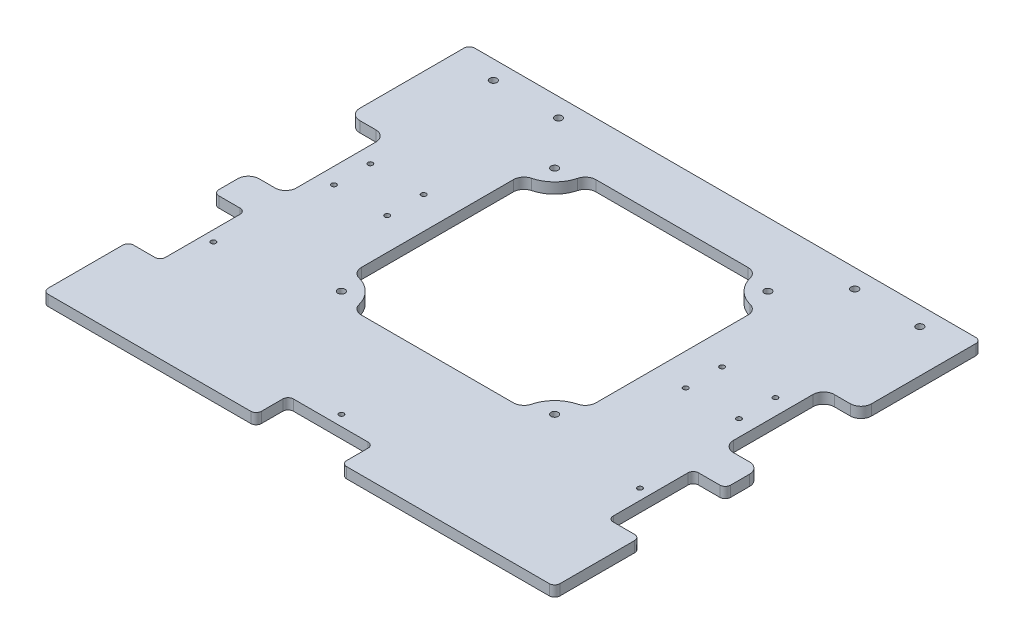
SolidWorks part; units mm, degrees
ref_plane "Front Plane" through (0, 0, 0) normal (0, 0, 1) x (1, 0, 0)
ref_plane "Top Plane" through (0, 0, 0) normal (0, 1, 0) x (1, 0, 0)
ref_plane "Right Plane" through (0, 0, 0) normal (1, 0, 0) x (0, 0, -1)
sketch "Footprint" plane through (0, 0, 0) normal (0, 1, 0) x (1, 0, 0)
  line L1 (-177.8, -177.8) -> (177.8, -177.8) construction
  line L2 (-177.8, -177.8) -> (-177.8, 177.8) construction
  line L3 (-177.8, 177.8) -> (177.8, 177.8) construction
  line L4 (177.8, -177.8) -> (177.8, 177.8) construction
  line L5 (-177.8, -177.8) -> (177.8, 177.8) construction
  line L6 (-177.8, 177.8) -> (177.8, -177.8) construction
  point P0 (0, 0)
  dimension "D1" = 355.6
  dimension "D2" = 355.6
sketch "Sketch2" plane through (0, 0, 0) normal (0, 1, 0) x (1, 0, 0)
  line L1 (-152.4, -152.4) -> (152.4, -152.4)
  line L2 (-152.4, -152.4) -> (-152.4, 101.6)
  line L3 (-152.4, 101.6) -> (152.4, 101.6)
  line L4 (152.4, -152.4) -> (152.4, 101.6)
  line L6 (0, 101.6) -> (0, 0) construction
  dimension "D1" = 254
  dimension "D2" = 304.8
  dimension "D3" = 101.6
extrude "Base" add sketch "Sketch2" along normal blind 6.35
sketch "Sketch5" plane through (0, 6.35, 0) normal (0, 1, 0) x (1, 0, 0)
  line L1 (-69.85, -69.85) -> (69.85, -69.85)
  line L2 (-69.85, -69.85) -> (-69.85, 69.85)
  line L3 (-69.85, 69.85) -> (69.85, 69.85)
  line L4 (69.85, -69.85) -> (69.85, 69.85)
  line L5 (-69.85, -69.85) -> (69.85, 69.85) construction
  line L6 (-69.85, 69.85) -> (69.85, -69.85) construction
  point P0 (0, 0)
  dimension "D1" = 139.7
  dimension "D2" = 139.7
extrude "Fan Cutout" cut sketch "Sketch5" against normal up to surface (6.35 mm away) up to face at (0, 0, 25.4)
sketch "Sketch7" plane through (0, 6.35, 0) normal (0, 1, 0) x (1, 0, 0)
  line L0 (-69.85, 50.8) -> (-69.85, 69.85)
  line L1 (50.8, 69.85) -> (69.85, 69.85)
  line L2 (-69.85, 69.85) -> (-69.85, -69.85) construction
  line L3 (-69.85, 69.85) -> (-50.8, 69.85)
  line L4 (69.85, 69.85) -> (69.85, 50.8)
  line L5 (69.85, 69.85) -> (-69.85, 69.85) construction
  line L6 (69.85, -69.85) -> (69.85, 69.85) construction
  line L7 (-69.85, -50.8) -> (-69.85, -69.85)
  line L8 (-69.85, -69.85) -> (-50.8, -69.85)
  line L9 (-69.85, -69.85) -> (69.85, -69.85) construction
  line L10 (50.8, -69.85) -> (69.85, -69.85)
  line L11 (69.85, -69.85) -> (69.85, -50.8)
  arc A0 (-69.85, 50.8) -> (-50.8, 69.85) centre (-69.85, 69.85) ccw
  arc A1 (50.8, 69.85) -> (69.85, 50.8) centre (69.85, 69.85) ccw
  arc A2 (-69.85, -50.8) -> (-50.8, -69.85) centre (-69.85, -69.85) cw
  arc A3 (50.8, -69.85) -> (69.85, -50.8) centre (69.85, -69.85) cw
  dimension "D3" = 19.05
  dimension "D6" = 19.05
  dimension "D9" = 19.05
  dimension "D12" = 19.05
  dimension "D1" = 19.05
  dimension "D2" = 19.05
  dimension "D4" = 19.05
  dimension "D5" = 19.05
  dimension "D7" = 19.05
  dimension "D8" = 19.05
  dimension "D10" = 19.05
  dimension "D11" = 19.05
extrude "Boss-Extrude1" add sketch "Sketch7" against normal up to surface (6.35 mm away) up to face at (0, 0, 0)
sketch "Sketch8" plane through (0, 6.35, 0) normal (0, 1, 0) x (1, 0, 0)
  line L0 (-69.85, 50.8) -> (-69.85, -50.8) construction
  line L1 (-63.5, -63.5) -> (63.5, -63.5) construction
  line L2 (-63.5, -63.5) -> (-63.5, 63.5) construction
  line L3 (-63.5, 63.5) -> (63.5, 63.5) construction
  line L4 (63.5, -63.5) -> (63.5, 63.5) construction
  line L5 (-63.5, -63.5) -> (63.5, 63.5) construction
  line L6 (-63.5, 63.5) -> (63.5, -63.5) construction
  line L7 (50.8, 69.85) -> (-50.8, 69.85) construction
  circle A0 centre (-63.5, 63.5) radius 2.1527
  circle A1 centre (63.5, 63.5) radius 2.1527
  circle A2 centre (63.5, -63.5) radius 2.1527
  circle A3 centre (-63.5, -63.5) radius 2.1527
  point P8 (0, 0)
  dimension "D1" = 4.3053
  dimension "D2" = 6.35
  dimension "D3" = 6.35
extrude "Cut-Extrude1" cut sketch "Sketch8" against normal up to surface (6.35 mm away) up to face at (0, 0, 0)
fillet "Fillet2" radius 6.35 8 edges at (69.85, 3.175, 50.8) (50.8, 3.175, 69.85) (69.85, 3.175, -50.8) (50.8, 3.175, -69.85) (-50.8, 3.175, 69.85) (-69.85, 3.175, 50.8) (-69.85, 3.175, -50.8) (-50.8, 3.175, -69.85)
sketch "Sketch3" plane through (0, 6.35, 0) normal (0, 1, 0) x (1, 0, 0)
  line L0 (-152.4, 101.6) -> (-152.4, -152.4) construction
  line L1 (-130.175, -30) -> (-152.4, -30)
  line L2 (-130.175, -30) -> (-130.175, 30)
  line L3 (-130.175, 30) -> (-152.4, 30)
  line L4 (-152.4, -30) -> (-152.4, 30)
  line L5 (-130.175, -30) -> (-152.4, 30) construction
  line L6 (-130.175, 30) -> (-152.4, -30) construction
  line L7 (152.4, -152.4) -> (152.4, 101.6) construction
  line L8 (130.175, -30) -> (152.4, -30)
  line L9 (130.175, -30) -> (130.175, 30)
  line L10 (130.175, 30) -> (152.4, 30)
  line L11 (152.4, -30) -> (152.4, 30)
  line L12 (130.175, -30) -> (152.4, 30) construction
  line L13 (130.175, 30) -> (152.4, -30) construction
  line L14 (-141.2875, 0) -> (141.2875, 0) construction
  point P0 (-141.2875, 0)
  point P7 (141.2875, 0)
  dimension "D1" = 60
  dimension "D2" = 22.225
extrude "Wheel Cutouts" cut sketch "Sketch3" against normal up to surface (6.35 mm away) up to face at (-63.5, 0, 61.3473)
fillet "Wheel Fillets" radius 6.35 8 edges at (152.4, 3.175, 30) (130.175, 3.175, 30) (130.175, 3.175, -30) (152.4, 3.175, -30) (-152.4, 3.175, 30) (-130.175, 3.175, 30) (-130.175, 3.175, -30) (-152.4, 3.175, -30)
sketch "Sketch4" plane through (0, 6.35, 0) normal (0, 1, 0) x (1, 0, 0)
  line L0 (-152.4, 101.6) -> (-152.4, 36.35) construction
  line L1 (-152.4, -50.8) -> (-133.35, -50.8)
  line L2 (-152.4, -50.8) -> (-152.4, -101.6)
  line L3 (-152.4, -101.6) -> (-133.35, -101.6)
  line L4 (-133.35, -50.8) -> (-133.35, -101.6)
  line L5 (152.4, -152.4) -> (152.4, -36.35) construction
  line L6 (152.4, -50.8) -> (133.35, -50.8)
  line L7 (152.4, -50.8) -> (152.4, -101.6)
  line L8 (152.4, -101.6) -> (133.35, -101.6)
  line L9 (133.35, -50.8) -> (133.35, -101.6)
  line L10 (-152.4, -152.4) -> (152.4, -152.4) construction
  line L11 (-25.4, -152.4) -> (25.4, -152.4)
  line L12 (-25.4, -152.4) -> (-25.4, -133.35)
  line L13 (-25.4, -133.35) -> (25.4, -133.35)
  line L14 (25.4, -152.4) -> (25.4, -133.35)
  line L15 (-133.35, -76.2) -> (-127, -76.2) construction
  line L16 (127, -76.2) -> (133.35, -76.2) construction
  line L17 (0, 0) -> (0, -133.35) construction
  circle A0 centre (-127, -76.2) radius 1.4732
  circle A1 centre (127, -76.2) radius 1.4732
  circle A2 centre (0, -127) radius 1.4732
  dimension "D9" = 2.9464
  dimension "D1" = 19.05
  dimension "D2" = 50.8
  dimension "D3" = 19.05
  dimension "D4" = 50.8
  dimension "D5" = 50.8
  dimension "D6" = 19.05
  dimension "D7" = 50.8
  dimension "D8" = 50.8
  dimension "D10" = 6.35
  dimension "D11" = 6.35
  dimension "D12" = 6.35
extrude "Ultrasonic Cutouts" cut sketch "Sketch4" against normal up to surface (6.35 mm away) up to face at (0, 0, 5.08)
fillet "Ultrasonic Fillets" radius 3.175 12 edges at (152.4, 3.175, 50.8) (133.35, 3.175, 50.8) (133.35, 3.175, 101.6) (152.4, 3.175, 101.6) (25.4, 3.175, 152.4) (25.4, 3.175, 133.35) (-25.4, 3.175, 133.35) (-25.4, 3.175, 152.4) (-152.4, 3.175, 101.6) (-133.35, 3.175, 101.6) (-152.4, 3.175, 50.8) (-133.35, 3.175, 50.8)
sketch "Sketch6" plane through (0, 6.35, 0) normal (0, 1, 0) x (1, 0, 0)
  line L0 (152.4, 101.6) -> (50.8, 101.6) construction
  line L1 (152.4, 101.6) -> (-152.4, 101.6) construction
  line L2 (50.8, 101.6) -> (-50.8, 101.6) construction
  line L3 (-50.8, 101.6) -> (-152.4, 101.6) construction
  line L4 (50.8, 101.6) -> (50.8, -152.4) construction
  line L5 (28.575, -152.4) -> (152.4, -152.4) construction
  line L6 (-50.8, 101.6) -> (-50.8, -152.4) construction
  line L7 (-152.4, -152.4) -> (-28.575, -152.4) construction
fillet "Fillet3" radius 3.175 4 edges at (-152.4, 3.175, 152.4) (152.4, 3.175, 152.4) (152.4, 3.175, -101.6) (-152.4, 3.175, -101.6)
sketch "Sketch9" plane through (0, 6.35, 0) normal (0, 1, 0) x (1, 0, 0)
  line L0 (-127, 90.4875) -> (-88.2, 90.4875) construction
  line L1 (149.225, 101.6) -> (-149.225, 101.6) construction
  line L2 (88.2, 90.4875) -> (127, 90.4875) construction
  line L3 (-152.4, 98.425) -> (-152.4, 36.35) construction
  line L4 (152.4, 36.35) -> (152.4, 98.425) construction
  circle A0 centre (-127, 90.4875) radius 2.1527
  circle A1 centre (-88.2, 90.4875) radius 2.1527
  circle A2 centre (88.2, 90.4875) radius 2.1527
  circle A3 centre (127, 90.4875) radius 2.1527
  dimension "D1" = 4.3053
  dimension "D2" = 38.8
  dimension "D3" = 38.8
  dimension "D4" = 11.1125
  dimension "D5" = 11.1125
  dimension "D6" = 25.4
  dimension "D7" = 25.4
extrude "Cut-Extrude2" cut sketch "Sketch9" against normal up to surface (6.35 mm away) up to face at (0, 0, 125.5268)
sketch "Sketch10" plane through (0, 6.35, 0) normal (0, 1, 0) x (1, 0, 0)
  circle A0 centre (-120.625, 10.85) radius 1.4732
  circle A1 centre (-88.875, 10.85) radius 1.4732
  circle A2 centre (-120.625, -10.85) radius 1.4732
  circle A3 centre (-88.875, -10.85) radius 1.4732
  circle A4 centre (88.875, 10.85) radius 1.4732
  circle A5 centre (120.625, 10.85) radius 1.4732
  circle A6 centre (88.875, -10.85) radius 1.4732
  circle A7 centre (120.625, -10.85) radius 1.4732
  arc A8 (-118.925, -10.85) -> (-122.325, -10.85) centre (-120.625, -10.85) ccw construction
  arc A9 (-87.175, -10.85) -> (-90.575, -10.85) centre (-88.875, -10.85) ccw construction
  arc A10 (-122.325, 10.85) -> (-118.925, 10.85) centre (-120.625, 10.85) ccw construction
  arc A11 (-90.575, 10.85) -> (-87.175, 10.85) centre (-88.875, 10.85) ccw construction
  arc A12 (122.325, -10.85) -> (118.925, -10.85) centre (120.625, -10.85) ccw construction
  arc A13 (90.575, -10.85) -> (87.175, -10.85) centre (88.875, -10.85) ccw construction
  arc A14 (87.175, 10.85) -> (90.575, 10.85) centre (88.875, 10.85) ccw construction
  arc A15 (118.925, 10.85) -> (122.325, 10.85) centre (120.625, 10.85) ccw construction
  dimension "D1" = 2.9464
extrude "Cut-Extrude3" cut sketch "Sketch10" against normal up to surface (6.35 mm away) up to face at (127, 0, -92.6402)
equation "\"WIDTH\"=14"
equation "\"TAB\"=0.75"
equation "\"D2@Sketch7\"=\"TAB\""
equation "\"D1@Sketch7\"=\"TAB\""
equation "\"D3@Sketch7\"=\"TAB\""
equation "\"D4@Sketch7\"=\"TAB\""
equation "\"D5@Sketch7\"=\"TAB\""
equation "\"D6@Sketch7\"=\"TAB\""
equation "\"D7@Sketch7\"=\"TAB\""
equation "\"D8@Sketch7\"=\"TAB\""
equation "\"D9@Sketch7\"=\"TAB\""
equation "\"D10@Sketch7\"=\"TAB\""
equation "\"D11@Sketch7\"=\"TAB\""
equation "\"D12@Sketch7\"=\"TAB\""
